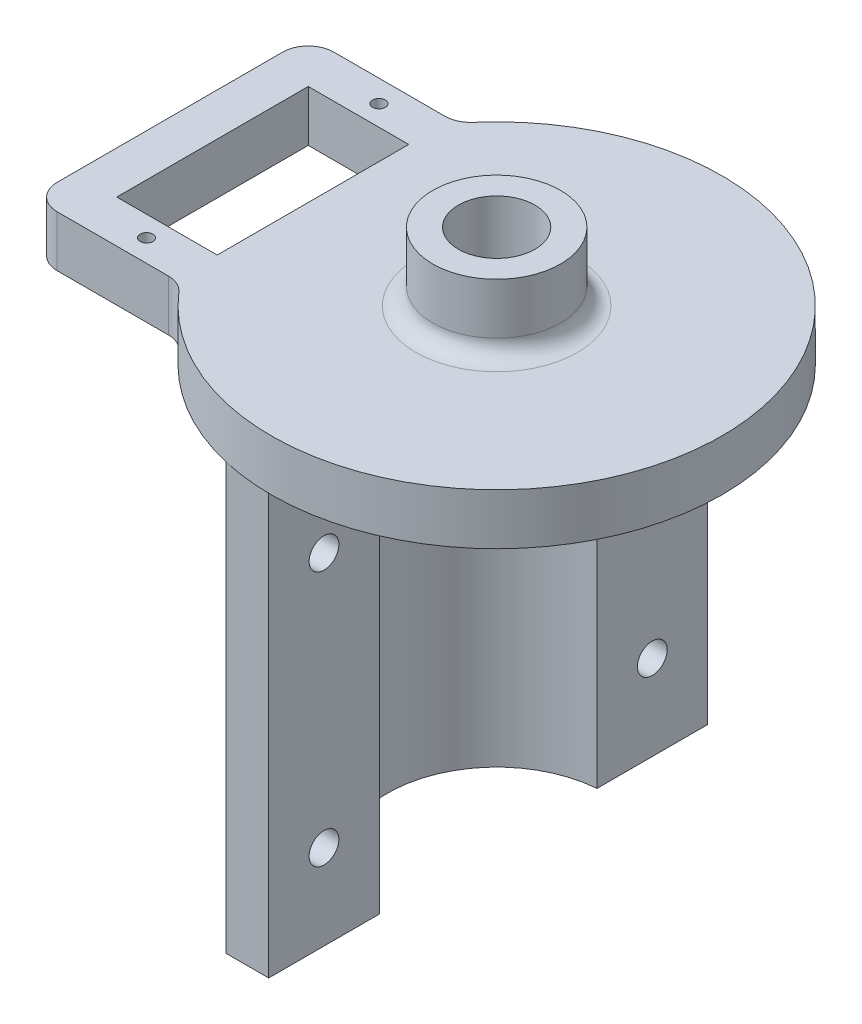
SolidWorks part; units mm, degrees
ref_plane "Front Plane" through (0, 0, 0) normal (0, 0, 1) x (1, 0, 0)
ref_plane "Top Plane" through (0, 0, 0) normal (0, 1, 0) x (1, 0, 0)
ref_plane "Right Plane" through (0, 0, 0) normal (1, 0, 0) x (0, 0, -1)
sketch "Sketch6" plane through (0, 0, 0) normal (0, -1, 0) x (1, 0, 0)
  line L5 (-1, 25.7848) -> (-1, 12.786)
  line L6 (-1, 25.7848) -> (-6, 25.7848)
  line L7 (-6, 25.7848) -> (-6, 16.7848)
  line L8 (-6, -16.7848) -> (-6, -25.7848)
  line L9 (-6, -25.7848) -> (-1, -25.7848)
  line L10 (-1, -25.7848) -> (-1, -12.786)
  line L11 (-12.825, 0) -> (-17.825, 0) construction
  arc A0 (-1, 12.786) -> (-1, -12.786) centre (0, 0) ccw
  arc A1 (-6, 16.7848) -> (-6, -16.7848) centre (0, 0) ccw
  dimension "D1" = 25.65
  dimension "D2" = 5
  dimension "D3" = 1
  dimension "D4" = 9
extrude "Boss-Extrude4" add sketch "Sketch6" along normal blind 50
sketch "Sketch7" plane through (-1, 0, 0) normal (1, 0, 0) x (0, 0, -1)
  line L0 (-19.2854, -50) -> (-19.2854, 0) construction
  line L3 (0, 0) -> (0, -50) construction
  line L6 (-25.7848, -25) -> (25.7848, -25) construction
  line L11 (-12.786, 0) -> (-25.7848, 0) construction
  line L12 (-12.786, -50) -> (-25.7848, -50) construction
  line L13 (-25.7848, -50) -> (-25.7848, 0) construction
  line L14 (25.7848, -50) -> (25.7848, 0) construction
  line L15 (-12.786, -50) -> (12.786, -50) construction
  circle A0 centre (-19.2854, -10) radius 1.75
  circle A1 centre (-19.2854, -40) radius 1.75
  circle A2 centre (19.2854, -40) radius 1.75
  circle A3 centre (19.2854, -10) radius 1.75
  dimension "D1" = 10
  dimension "D2" = 3.5
extrude "Cut-Extrude1" cut sketch "Sketch7" against normal through all
sketch "Sketch8" plane through (0, 0, 0) normal (0, 1, 0) x (1, 0, 0)
  line L0 (-27.4841, -13.65) -> (-27.4841, 13.65) construction
  line L1 (-33.3841, -11.25) -> (-21.5841, -11.25)
  line L2 (-33.3841, -11.25) -> (-33.3841, 11.25)
  line L3 (-33.3841, 11.25) -> (-21.5841, 11.25)
  line L4 (-21.5841, -11.25) -> (-21.5841, 11.25)
  line L5 (-35.3841, -16.25) -> (-22.319, -16.25)
  line L6 (-38.3841, -13.25) -> (-38.3841, 13.25)
  line L7 (-35.3841, 16.25) -> (-22.319, 16.25)
  circle A1 centre (-27.4841, 13.65) radius 0.75
  circle A2 centre (-27.4841, -13.65) radius 0.75
  arc A3 (-20.0472, -17.2906) -> (-20.0472, 17.2906) centre (0, 0) ccw
  arc A4 (-35.3841, -16.25) -> (-38.3841, -13.25) centre (-35.3841, -13.25) cw
  arc A5 (-38.3841, 13.25) -> (-35.3841, 16.25) centre (-35.3841, 13.25) cw
  arc A6 (-22.319, 16.25) -> (-20.0472, 17.2906) centre (-22.319, 19.25) ccw
  arc A7 (-22.319, -16.25) -> (-20.0472, -17.2906) centre (-22.319, -19.25) cw
  circle A8 centre (-27.4841, 5.35) radius 5.9 construction
  point P7 (-21.5841, 0)
  point P13 (-27.4841, -11.25)
  point P18 (-27.4841, 0)
  point P24 (-38.3841, 0)
  dimension "D1" = 5
  dimension "D4" = 1.5
  dimension "D7" = 5
  dimension "D8" = 3
  dimension "D9" = 3
  dimension "D10" = 11.8
  dimension "D2" = 11.8
  dimension "D3" = 22.5
  dimension "D5" = 27.3
  dimension "D6" = 28
extrude "Boss-Extrude5" add sketch "Sketch8" along normal blind 6
sketch "Sketch9" plane through (0, 6, 0) normal (0, 1, 0) x (1, 0, 0)
  circle A0 centre (0, 0) radius 7.5
  dimension "D1" = 15
extrude "Boss-Extrude6" add sketch "Sketch9" along normal blind 8
fillet "Fillet1" radius 2 1 edges at (0, 6, 7.5)
sketch "Sketch10" plane through (0, 14, 0) normal (0, 1, 0) x (1, 0, 0)
  circle A0 centre (0, 0) radius 4.5
  dimension "D1" = 9
extrude "Cut-Extrude2" cut sketch "Sketch10" against normal through all
